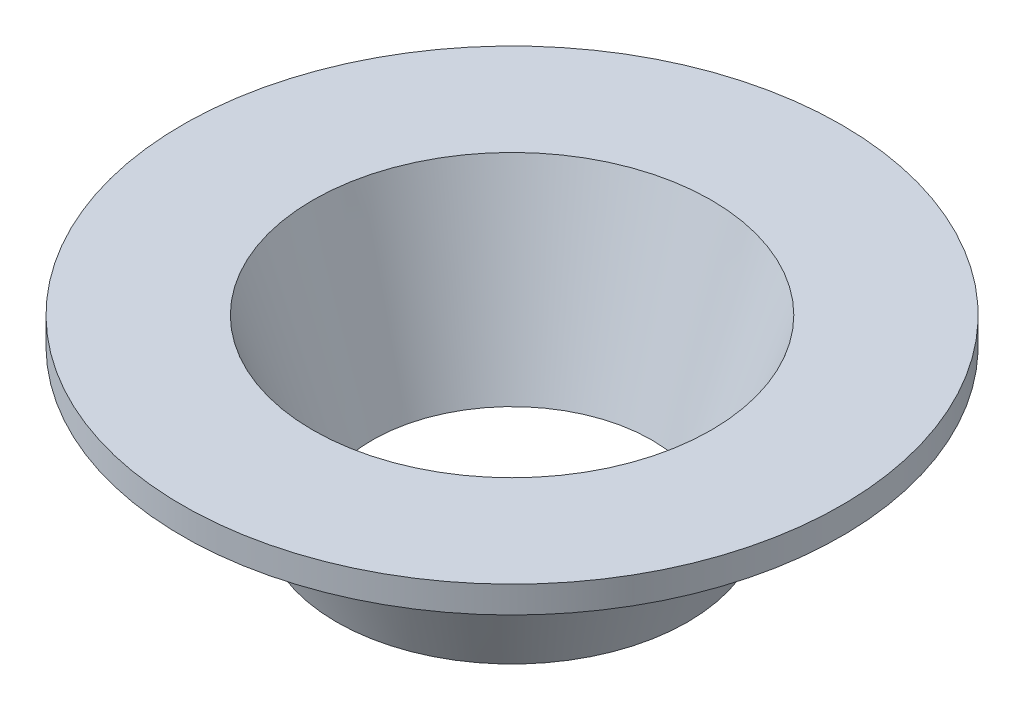
SolidWorks part; units mm, degrees
material "AISI 316 Stainless Steel Sheet (SS)"
ref_plane "Front Plane" through (0, 0, 0) normal (0, 0, 1) x (1, 0, 0)
ref_plane "Top Plane" through (0, 0, 0) normal (0, 1, 0) x (1, 0, 0)
ref_plane "Right Plane" through (0, 0, 0) normal (1, 0, 0) x (0, 0, -1)
sketch "Sketch1" plane through (0, 0, 0) normal (0, 0, 1) x (1, 0, 0)
  line L0 (0, 0) -> (0, 10) construction
  line L1 (-2, 0) -> (-4, 0)
  line L2 (-4, 0) -> (-7.15, 8.5)
  line L3 (-7.15, 8.5) -> (-12.65, 8.5)
  line L4 (-12.65, 8.5) -> (-12.65, 10)
  line L5 (-12.65, 10) -> (-5.3333, 10)
  line L6 (-5.3333, 10) -> (-2, 0)
  line L7 (-2, 0) -> (0, 0) construction
  line L8 (0, 0) -> (0, 6) construction
  line L9 (0, 6) -> (-4, 6) construction
  line L10 (-4, 6) -> (-2, 0) construction
  line L11 (5.85, -1.3087) -> (5.85, 17.0497) construction
  point P13 (-4, 0)
  point P14 (-4, 0)
  point P15 (-17.2228, 8.5)
  dimension "D1" = 18.5
  dimension "D2" = 1.5
  dimension "D3" = 2
  dimension "D4" = 10
  dimension "D5" = 4
  dimension "D6" = 6
  dimension "D7" = 2
  dimension "D8" = 5.5
  dimension "D9" = 9.85
revolve "Revolve1" add sketch "Sketch1" angle 360 about L11
